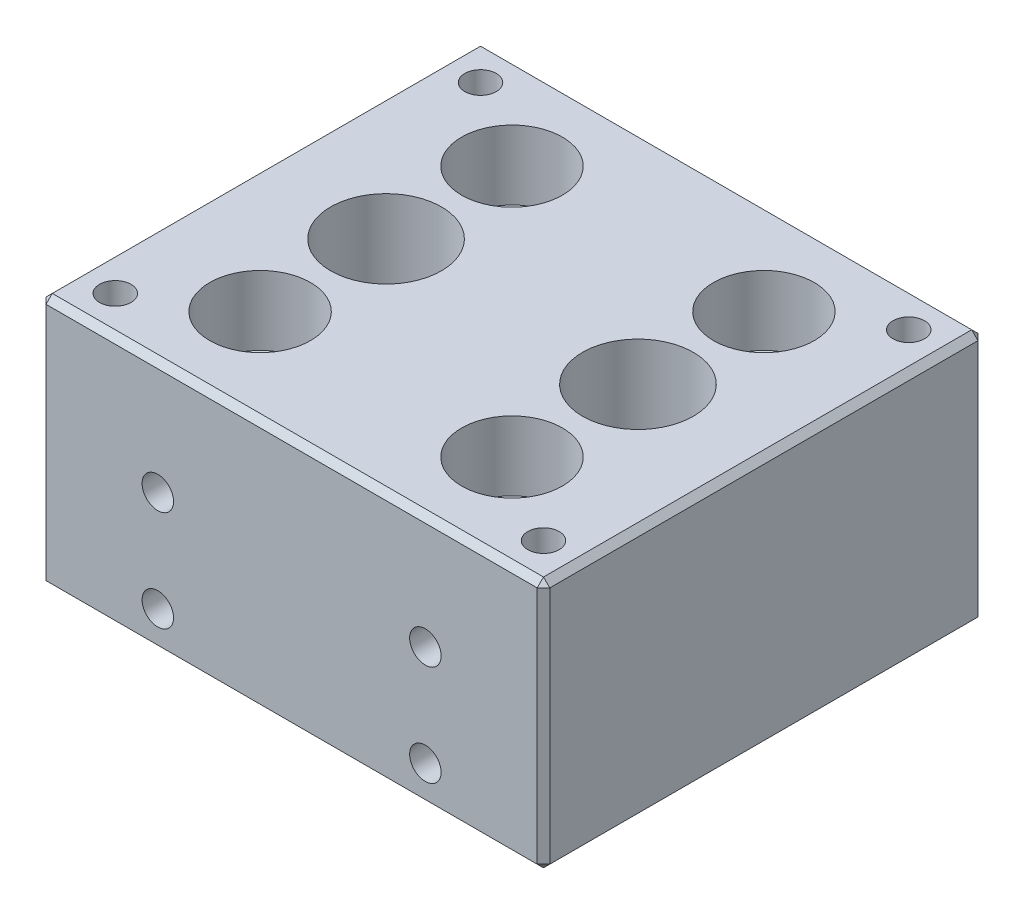
SolidWorks part; units mm, degrees
material "AISI 304"
ref_plane "Front Plane" through (0, 0, 0) normal (0, 0, 1) x (1, 0, 0)
ref_plane "Top Plane" through (0, 0, 0) normal (0, 1, 0) x (1, 0, 0)
ref_plane "Right Plane" through (0, 0, 0) normal (1, 0, 0) x (0, 0, -1)
sketch "Sketch1" plane through (0, 0, 0) normal (0, 1, 0) x (1, 0, 0)
  line L1 (-20, -17.5) -> (20, -17.5)
  line L2 (-20, -17.5) -> (-20, 17.5)
  line L3 (-20, 17.5) -> (20, 17.5)
  line L4 (20, -17.5) -> (20, 17.5)
  line L5 (-20, -17.5) -> (20, 17.5) construction
  line L6 (-20, 17.5) -> (20, -17.5) construction
  point P0 (0, 0)
  dimension "D1" = 35
  dimension "D2" = 40
extrude "Boss-Extrude1" add sketch "Sketch1" along normal blind 20
hole_wizard "Tap Drill for M3x0.5 Tap1" positions "Sketch4" profile "Sketch3" hole size "M3x0.5" standard "ANSI Metric"
sketch "Sketch4" plane through (0, 20, 0) normal (0, 1, 0) x (1, 0, 0)
  line L1 (17, -14.5) -> (-17, -14.5) construction
  line L2 (17, -14.5) -> (17, 14.5) construction
  line L3 (17, 14.5) -> (-17, 14.5) construction
  line L4 (-17, -14.5) -> (-17, 14.5) construction
  line L5 (17, -14.5) -> (-17, 14.5) construction
  line L6 (17, 14.5) -> (-17, -14.5) construction
  point P0 (-17, 14.5)
  point P2 (17, 14.5)
  point P4 (17, -14.5)
  point P6 (-17, -14.5)
  dimension "D1" = 34
  dimension "D2" = 29
sketch "Sketch3" plane through (-17, 20, -14.5) normal (1, 0, 0) x (0, 0, 1)
  line L0 (0, 0) -> (0, 4)
  line L1 (0, 4) -> (1.25, 4)
  line L2 (1.25, 4) -> (1.25, 0)
  line L5 (1.25, 0) -> (0, 0)
  line L10 (0, 4) -> (-1.25, 4) construction
  line L11 (0, -6.35) -> (0, 107.95) construction
  dimension "Hole Dia." = 2.5
  dimension "Hole Depth" = 4
  dimension "Drill Angle" = 180
hole_wizard "Ø8.4 (8.4) Diameter Hole2" positions "Sketch9" profile "Sketch8" hole size "Ø8.4" standard "ANSI Metric"
sketch "Sketch9" plane through (0, 20, 0) normal (0, 1, 0) x (1, 0, 0)
  line L0 (-10, 0) -> (10, 0) construction
  point P0 (-10, 0)
  point P2 (10, 0)
  dimension "D1" = 20
sketch "Sketch8" plane through (-10, 20, 0) normal (1, 0, 0) x (0, 0, 1)
  line L0 (0, 0) -> (0, 17.5236)
  line L1 (0, 17.5236) -> (4.2, 15)
  line L2 (4.2, 15) -> (4.2, 0)
  line L5 (4.2, 0) -> (0, 0)
  line L10 (0, 17.5236) -> (-4.2, 15) construction
  line L11 (0, -6.35) -> (0, 107.95) construction
  dimension "Hole Dia." = 8.4
  dimension "Hole Depth" = 15
  dimension "Drill Angle" = 118
hole_wizard "Ø8.4 (8.4) Diameter Hole1" positions "Sketch11" profile "Sketch10" hole size "Ø8.4" standard "ANSI Metric"
sketch "Sketch11" plane through (-20, 0, 0) normal (-1, 0, 0) x (0, 0, 1)
  point P0 (0, 5)
  dimension "D1" = 5
sketch "Sketch10" plane through (-20, 5, 0) normal (0, 1, 0) x (0, 0, 1)
  line L0 (0, 0) -> (0, 37.5236)
  line L1 (0, 37.5236) -> (4.2, 35)
  line L2 (4.2, 35) -> (4.2, 0)
  line L5 (4.2, 0) -> (0, 0)
  line L10 (0, 37.5236) -> (-4.2, 35) construction
  line L11 (0, -6.35) -> (0, 107.95) construction
  dimension "Hole Dia." = 8.4
  dimension "Hole Depth" = 35
  dimension "Drill Angle" = 118
hole_wizard "Ø7.0 (7) Diameter Hole1" positions "Sketch13" profile "Sketch12" hole size "Ø7.0" standard "ANSI Metric"
sketch "Sketch13" plane through (0, 0, 0) normal (0, -1, 0) x (-1, 0, 0)
  line L1 (-10, 10) -> (10, 10)
  line L2 (-10, 10) -> (-10, -10)
  line L3 (-10, -10) -> (10, -10)
  line L4 (10, 10) -> (10, -10)
  line L5 (-10, 10) -> (10, -10) construction
  line L6 (-10, -10) -> (10, 10) construction
  point P0 (10, -10)
  point P2 (-10, -10)
  point P4 (-10, 10)
  point P6 (10, 10)
  dimension "D1" = 20
  dimension "D2" = 20
sketch "Sketch12" plane through (-10, 0, 10) normal (1, 0, 0) x (0, 0, -1)
  line L0 (0, 0) -> (0, 17.103)
  line L1 (0, 17.103) -> (3.5, 15)
  line L2 (3.5, 15) -> (3.5, 0)
  line L5 (3.5, 0) -> (0, 0)
  line L10 (0, 17.103) -> (-3.5, 15) construction
  line L11 (0, -6.35) -> (0, 107.95) construction
  dimension "Hole Dia." = 7
  dimension "Hole Depth" = 15
  dimension "Drill Angle" = 118
hole_wizard "Ø8.0 (8) Diameter Hole1" positions "Sketch15" profile "Sketch14" hole size "Ø8.0" standard "ANSI Metric"
sketch "Sketch15" plane through (0, 20, 0) normal (0, 1, 0) x (1, 0, 0)
  point P0 (-10, 10)
  point P3 (10, 10)
  point P6 (10, -10)
  point P9 (-10, -10)
sketch "Sketch14" plane through (-10, 20, -10) normal (1, 0, 0) x (0, 0, 1)
  line L0 (0, 0) -> (0, 5.5)
  line L1 (0, 5.5) -> (4, 5.5)
  line L2 (4, 5.5) -> (4, 0)
  line L5 (4, 0) -> (0, 0)
  line L10 (0, 5.5) -> (-4, 5.5) construction
  line L11 (0, -6.35) -> (0, 107.95) construction
  dimension "Hole Dia." = 8
  dimension "Hole Depth" = 5.5
  dimension "Drill Angle" = 180
hole_wizard "Tap Drill for M3x0.5 Tap2" positions "Sketch17" profile "Sketch16" hole size "M3x0.5" standard "ANSI Metric"
sketch "Sketch17" plane through (0, 0, 17.5) normal (0, 0, 1) x (1, 0, 0)
  line L1 (-10.6221, 11) -> (10.6221, 11)
  line L2 (-10.6221, 11) -> (-10.6221, 3)
  line L3 (-10.6221, 3) -> (10.6221, 3)
  line L4 (10.6221, 11) -> (10.6221, 3)
  line L5 (-10.6221, 11) -> (10.6221, 3) construction
  line L6 (-10.6221, 3) -> (10.6221, 11) construction
  line L7 (0, 7) -> (0, 0) construction
  point P0 (-10.6221, 11)
  point P2 (-10.6221, 3)
  point P4 (10.6221, 3)
  point P6 (10.6221, 11)
  dimension "D1" = 21.2443
  dimension "D2" = 3
  dimension "D3" = 8
sketch "Sketch16" plane through (-10.6221, 11, 17.5) normal (1, 0, 0) x (0, -1, 0)
  line L0 (0, 0) -> (0, 5.5)
  line L1 (0, 5.5) -> (1.25, 5.5)
  line L2 (1.25, 5.5) -> (1.25, 0)
  line L5 (1.25, 0) -> (0, 0)
  line L10 (0, 5.5) -> (-1.25, 5.5) construction
  line L11 (0, -6.35) -> (0, 107.95) construction
  dimension "Hole Dia." = 2.5
  dimension "Hole Depth" = 5.5
  dimension "Drill Angle" = 180
mirror "Mirror1" about plane through (0, 0, 0) normal (0, 0, 1) of "Tap Drill for M3x0.5 Tap2"
chamfer "Chamfer1" distance 0.5 angle 45 12 edges at (0, 20, -17.5) (0, 0, -17.5) (20, 0, 0) (20, 10, -17.5) (20, 20, 0) (20, 10, 17.5) (-20, 0, 0) (-20, 10, -17.5) (0, 0, 17.5) (-20, 20, 0) (0, 20, 17.5) (-20, 10, 17.5)
hole_wizard "G1/8 Tapped Hole1" positions "Sketch19" profile "Sketch18" tap size "G1/8" standard "GB"
sketch "Sketch19" plane through (0, 20, 0) normal (0, 1, 0) x (1, 0, 0)
  point P0 (-10, 0)
  point P7 (10, 0)
sketch "Sketch18" plane through (-10, 20, 0) normal (1, 0, 0) x (0, 0, 1)
  line L0 (0, 0) -> (0, 10)
  line L1 (0, 10) -> (4.4, 10)
  line L2 (4.4, 10) -> (4.4, 0)
  line L5 (4.4, 0) -> (0, 0)
  line L10 (0, 10) -> (-4.4, 10) construction
  line L11 (0, -6.35) -> (0, 107.95) construction
  dimension "Tap Drill Dia." = 8.8
  dimension "Tap Drill Depth" = 10
  dimension "Drill Angle" = 180
